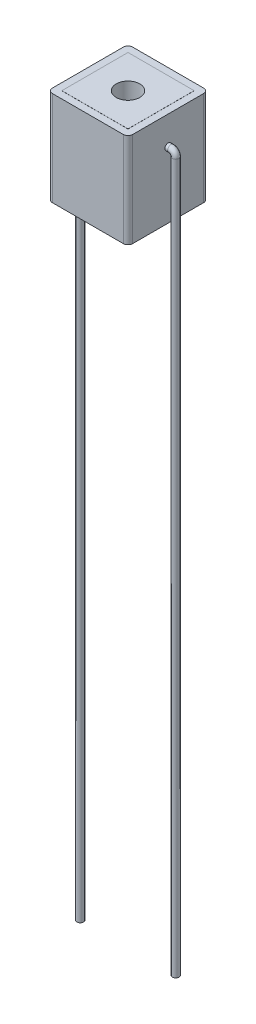
SolidWorks part; units mm, degrees
ref_plane "Front Plane" through (0, 0, 0) normal (0, 0, 1) x (1, 0, 0)
ref_plane "Top Plane" through (0, 0, 0) normal (0, 1, 0) x (1, 0, 0)
ref_plane "Right Plane" through (0, 0, 0) normal (1, 0, 0) x (0, 0, -1)
sketch "Sketch1" plane through (0, 0, 0) normal (0, 1, 0) x (1, 0, 0)
  line L1 (-4.25, 4.25) -> (4.25, 4.25)
  line L2 (-4.25, 4.25) -> (-4.25, -4.25)
  line L3 (-4.25, -4.25) -> (4.25, -4.25)
  line L4 (4.25, 4.25) -> (4.25, -4.25)
  line L5 (-4.25, 4.25) -> (4.25, -4.25) construction
  line L6 (-4.25, -4.25) -> (4.25, 4.25) construction
  point P0 (0, 0)
  dimension "D1" = 8.5
  dimension "D2" = 8.5
sketch "Sketch2" plane through (0, 0, 0) normal (0, 1, 0) x (1, 0, 0)
  line L1 (-3.5, 3.5) -> (3.5, 3.5)
  line L2 (-3.5, 3.5) -> (-3.5, -3.5)
  line L3 (-3.5, -3.5) -> (3.5, -3.5)
  line L4 (3.5, 3.5) -> (3.5, -3.5)
  line L5 (-3.5, 3.5) -> (3.5, -3.5) construction
  line L6 (-3.5, -3.5) -> (3.5, 3.5) construction
  point P0 (0, 0)
  dimension "D1" = 7
  dimension "D2" = 7
extrude "Boss-Extrude1" add sketch "Sketch1" along normal blind 10
extrude "Boss-Extrude2" add sketch "Sketch2" along normal blind 10.01 and the other way blind 0.01
fillet "Fillet2" radius 0.5 4 edges at (4.25, 5, 4.25) (-4.25, 5, 4.25) (-4.25, 5, -4.25) (4.25, 5, -4.25)
sketch "Sketch35" plane through (0, 10.01, 0) normal (0, 1, 0) x (1, 0, 0)
  circle A0 centre (0, 0) radius 1.25
  dimension "D1" = 2.5
extrude "Cut-Extrude1" cut sketch "Sketch35" against normal blind 20
sketch "Sketch36" plane through (4.25, 0, 0) normal (1, 0, 0) x (0, 0, -1)
  line L0 (-3.75, 10) -> (3.75, 10) construction
  point P0 (0, 7)
  dimension "D1" = 3
ref_plane "Plane1" through (0, 0, 0) normal (0, 0, 1) x (1, 0, 0)
sketch "Sketch37" plane through (0, 0, 0) normal (0, 0, 1) x (1, 0, 0)
  line L0 (4.25, 7) -> (4.55, 7)
  line L3 (5.05, 6.5) -> (5.05, -68.5)
  arc A1 (5.05, 6.5) -> (4.55, 7) centre (4.55, 6.5) ccw
  dimension "D2" = 0.5
  dimension "D1" = 0.3
  dimension "D3" = 75
sweep "Sweep1" add path "Sketch37" circular profile diameter 0.7 parameters "D3"=0.7
mirror "Mirror1" about plane through (0, 0, 0) normal (1, 0, 0) of "Sweep1"
